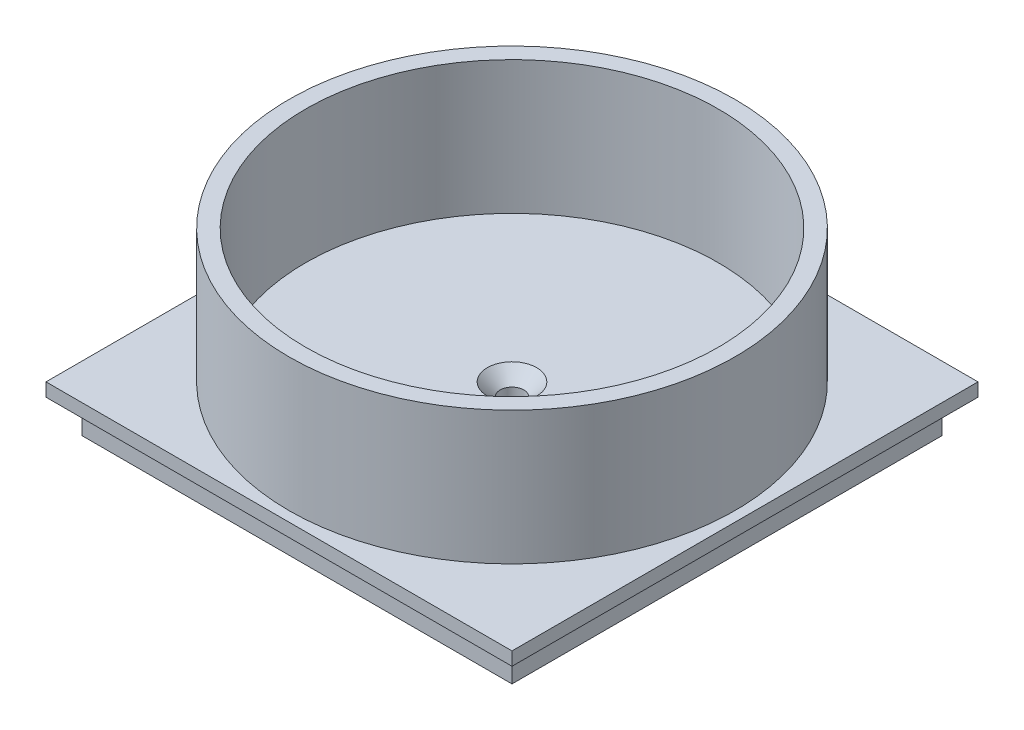
SolidWorks part; units mm, degrees
ref_plane "Front Plane" through (0, 0, 0) normal (0, 0, 1) x (1, 0, 0)
ref_plane "Top Plane" through (0, 0, 0) normal (0, 1, 0) x (1, 0, 0)
ref_plane "Right Plane" through (0, 0, 0) normal (1, 0, 0) x (0, 0, -1)
sketch "Sketch1" plane through (0, 0, 0) normal (0, 1, 0) x (1, 0, 0)
  line L1 (0, 0) -> (82.042, 0)
  line L2 (0, 0) -> (0, 82.042)
  line L3 (0, 82.042) -> (82.042, 82.042)
  line L4 (82.042, 0) -> (82.042, 82.042)
  dimension "D1" = 82.042
  dimension "D2" = 82.042
extrude "Boss-Extrude1" add sketch "Sketch1" along normal blind 6.35
sketch "Sketch3" plane through (0, 6.35, 0) normal (0, 1, 0) x (1, 0, 0)
  line L0 (0, 82.042) -> (0, 0) construction
  line L1 (-3.429, 85.471) -> (85.471, 85.471)
  line L2 (-3.429, 85.471) -> (-3.429, -3.429)
  line L3 (-3.429, -3.429) -> (85.471, -3.429)
  line L4 (85.471, 85.471) -> (85.471, -3.429)
  line L5 (82.042, 82.042) -> (0, 82.042) construction
  point P4 (0, 41.021)
  point P7 (-3.429, 41.021)
  point P10 (41.021, 82.042)
  point P11 (41.021, 85.471)
  dimension "D1" = 88.9
  dimension "D2" = 88.9
extrude "Boss-Extrude3" add sketch "Sketch3" along normal blind 2.54
sketch "Sketch4" plane through (0, 8.89, 0) normal (0, 1, 0) x (1, 0, 0)
  line L0 (-3.429, 85.471) -> (-3.429, -3.429) construction
  line L1 (85.471, 85.471) -> (-3.429, 85.471) construction
  circle A0 centre (41.021, 41.021) radius 2.25
  dimension "D1" = 44.45
  dimension "D3" = 4.5
  dimension "D2" = 44.45
extrude "Cut-Extrude1" cut sketch "Sketch4" against normal through all
sketch "Sketch5" plane through (0, 8.89, 0) normal (0, 1, 0) x (1, 0, 0)
  circle A0 centre (41.021, 41.021) radius 39.37
  circle A1 centre (41.021, 41.021) radius 42.545
  dimension "D1" = 78.74
  dimension "D2" = 3.175
extrude "Boss-Extrude4" add sketch "Sketch5" along normal blind 25.4
hole_wizard "CSK for M4 Flat Head Machine Screw1" positions "Sketch6" profile "Sketch7" countersink size "M4" standard "ANSI Metric"
sketch "Sketch6" plane through (0, 8.89, 0) normal (0, 1, 0) x (1, 0, 0)
  point P0 (41.021, 41.021)
sketch "Sketch7" plane through (41.021, 8.89, -41.021) normal (1, 0, 0) x (0, 0, 1)
  line L0 (0, 0) -> (0, 5.3519)
  line L1 (0, 5.3519) -> (2.25, 4)
  line L2 (2.25, 4) -> (2.25, 2.45)
  line L3 (2.25, 2.45) -> (4.7, 0)
  line L5 (4.7, 0) -> (0, 0)
  line L6 (-2.25, 2.45) -> (-4.7, 0) construction
  line L10 (0, 5.3519) -> (-2.25, 4) construction
  line L11 (0, -6.35) -> (0, 107.95) construction
  dimension "Hole Dia." = 4.5
  dimension "Hole Depth" = 4
  dimension "Near C'Sink Dia." = 9.4
  dimension "Near C'Sink Angle" = 90
  dimension "Drill Angle" = 118
